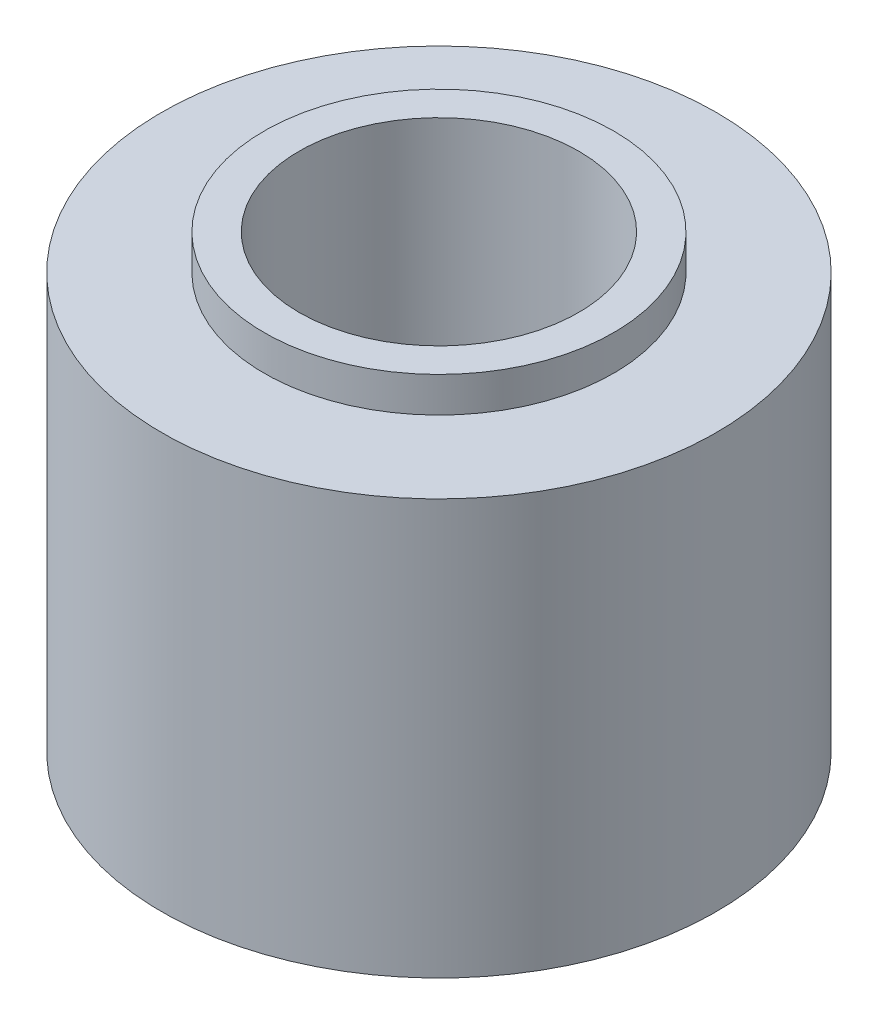
SolidWorks part; units mm, degrees
material "Plain Carbon Steel"
ref_plane "Front Plane" through (0, 0, 0) normal (0, 0, 1) x (1, 0, 0)
ref_plane "Top Plane" through (0, 0, 0) normal (0, 1, 0) x (1, 0, 0)
ref_plane "Right Plane" through (0, 0, 0) normal (1, 0, 0) x (0, 0, -1)
sketch "Sketch1" plane through (0, 0, 0) normal (0, 0, 1) x (1, 0, 0)
  line L0 (0, 5.5562) -> (0, -5.5562) construction
  line L1 (3.2004, 5.5562) -> (6.35, 5.5562)
  line L2 (3.2004, 5.5562) -> (3.2004, -5.5562)
  line L3 (3.2004, -5.5562) -> (6.35, -5.5562)
  line L4 (6.35, 5.5562) -> (6.35, -5.5562)
  line L5 (0, 0) -> (3.2004, 0) construction
  dimension "D1" = 11.1125
  dimension "D2" = 6.4008
  dimension "D3" = 12.7
revolve "Revolve1" add sketch "Sketch1" angle 360 about L0
sketch "Sketch2" plane through (0, 0, 0) normal (0, 0, 1) x (1, 0, 0)
  line L0 (0, 0) -> (-10.9511, 0) construction
  line L1 (-6.35, 5.5562) -> (-4, 5.5562)
  line L2 (-6.35, 5.5562) -> (-6.35, 4.75)
  line L3 (-6.35, 4.75) -> (-4, 4.75)
  line L4 (-4, 5.5562) -> (-4, 4.75)
  line L5 (-6.35, 5.5562) -> (-6.35, -5.5562) construction
  line L6 (-6.35, -5.5562) -> (-4, -5.5562)
  line L7 (-6.35, -5.5562) -> (-6.35, -4.75)
  line L8 (-6.35, -4.75) -> (-4, -4.75)
  line L9 (-4, -5.5562) -> (-4, -4.75)
  line L10 (-6.35, -5.5562) -> (6.35, -5.5562) construction
  line L11 (6.35, 5.5562) -> (-6.35, 5.5562) construction
  line L12 (0, -6.0449) -> (0, 6.0159) construction
  dimension "D1" = 9.5
  dimension "D2" = 8
revolve "Cut-Revolve1" cut sketch "Sketch2" angle 360 about L12
